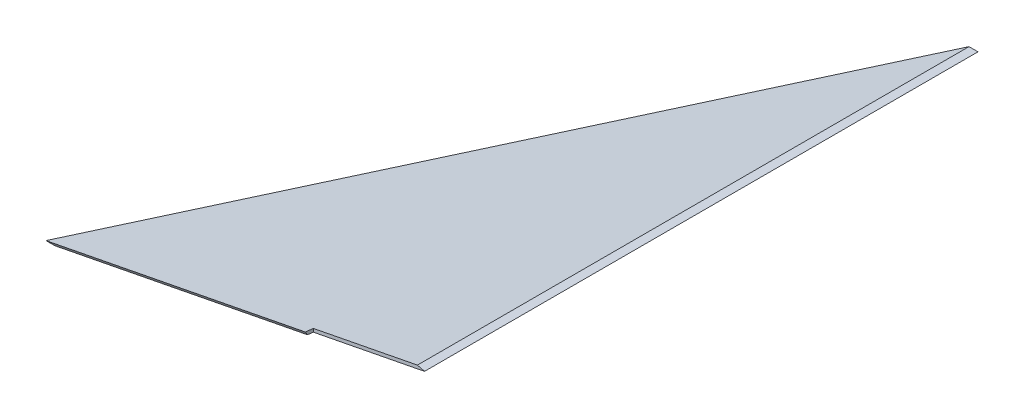
SolidWorks part; units mm, degrees
ref_plane "Front Plane" through (0, 0, 0) normal (0, 0, 1) x (1, 0, 0)
ref_plane "Top Plane" through (0, 0, 0) normal (0, 1, 0) x (1, 0, 0)
ref_plane "Right Plane" through (0, 0, 0) normal (1, 0, 0) x (0, 0, -1)
sketch "Sketch1" plane through (0, 0, 0) normal (1, 0, 0) x (0, 0, -1)
  line L0 (0, 0) -> (-197.18, 0)
  line L1 (-197.18, 0) -> (-162.9401, -59.3053)
  line L2 (-162.9401, -59.3053) -> (0, 0)
  dimension "D1" = 20
  dimension "D2" = 60
  dimension "D3" = 197.18
extrude "Boss-Extrude1" add sketch "Sketch1" along normal blind 304.8
sketch "Sketch2" plane through (0, 0, 0) normal (0, 0, 1) x (1, 0, 0)
  line L4 (304.8, 0) -> (0, 0) construction
  line L5 (152.4, 0) -> (152.4, 50000) construction
  line L8 (138.6849, -59.3053) -> (301.625, 0)
  line L9 (304.8, 0) -> (141.8599, -59.3053)
  line L11 (304.8, -59.3053) -> (0, -59.3053) construction
  line L12 (138.6849, -59.3053) -> (0, -59.3053)
  line L13 (0, -59.3053) -> (0, 0)
  line L14 (0, 0) -> (301.625, 0)
  line L15 (304.8, 0) -> (304.8, -59.3053)
  line L16 (304.8, -59.3053) -> (141.8599, -59.3053)
  point P10 (152.4, 0)
  dimension "D1" = 3.175
  dimension "D2" = 20
extrude "Cut-Extrude1" cut sketch "Sketch2" against normal through all and the other way through all
sketch "Sketch3" plane through (0, 0, 0) normal (0, 1, 0) x (1, 0, 0)
  line L0 (301.625, -197.18) -> (254.5961, -187.2974)
  line L1 (301.625, -197.18) -> (138.6849, -162.9401) construction
  line L2 (254.5961, -187.2974) -> (255.0858, -184.9671)
  line L3 (255.0858, -184.9671) -> (304.8, -195.4139)
  line L5 (304.8, 0) -> (304.8, -197.18) construction
  line L6 (304.8, -195.4139) -> (304.8, -197.18)
  line L7 (304.8, -197.18) -> (301.625, -197.18)
  line L8 (254.5961, -187.2974) -> (301.625, -197.18)
  line M4 (301.625, 0) -> (301.625, -197.18)
  line M5 (301.625, -197.18) -> (304.8, -197.18)
  line M6 (304.8, -197.18) -> (304.8, 0)
  dimension "D1" = 2.3813
  dimension "D2" = 50.8
extrude "Cut-Extrude2" cut sketch "Sketch3" against normal through all contours L3 L2 L0 M4 | L3 M4 M5 M6
